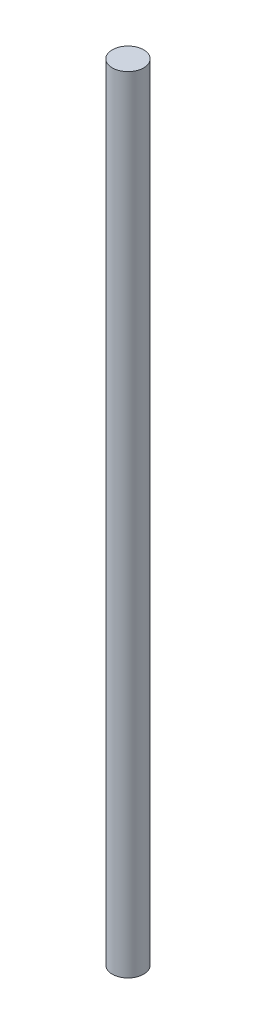
SolidWorks part; units mm, degrees
ref_plane "前视基准面" through (0, 0, 0) normal (0, 0, 1) x (1, 0, 0)
ref_plane "上视基准面" through (0, 0, 0) normal (0, 1, 0) x (1, 0, 0)
ref_plane "右视基准面" through (0, 0, 0) normal (1, 0, 0) x (0, 0, -1)
sketch "草图1" plane through (0, 0, 0) normal (0, 1, 0) x (1, 0, 0)
  circle A0 centre (0, 0) radius 4
extrude "凸台-拉伸1" add sketch "草图1" along normal blind 200
